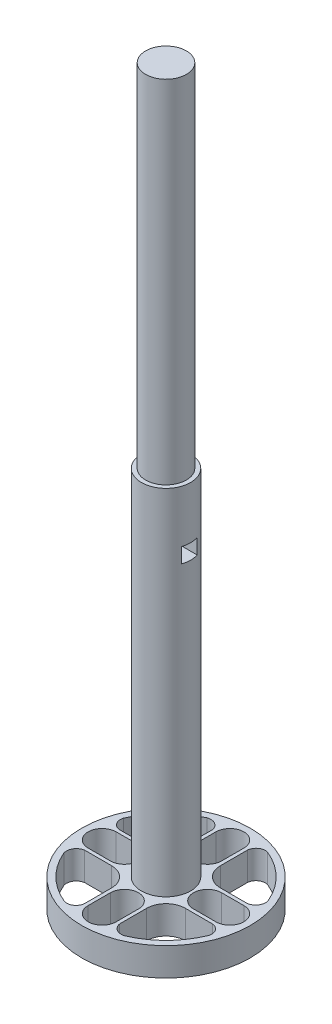
SolidWorks part; units mm, degrees
ref_plane "Front Plane" through (0, 0, 0) normal (0, 0, 1) x (1, 0, 0)
ref_plane "Top Plane" through (0, 0, 0) normal (0, 1, 0) x (1, 0, 0)
ref_plane "Right Plane" through (0, 0, 0) normal (1, 0, 0) x (0, 0, -1)
sketch "Sketch1" plane through (0, 0, 0) normal (0, 1, 0) x (1, 0, 0)
  line L0 (0, -9.0866) -> (0, -5.9134) construction
  line L1 (-9.0866, 0) -> (-5.9134, 0) construction
  line L2 (0, -13.2) -> (0, 13.2) construction
  line L3 (-2, -9.0866) -> (-2, -5.9134)
  line L4 (2, -9.0866) -> (2, -5.9134)
  line L5 (-9.0866, 2) -> (-5.9134, 2)
  line L6 (-9.0866, -2) -> (-5.9134, -2)
  line L7 (0, 9.0866) -> (0, 5.9134) construction
  line L8 (2, 9.0866) -> (2, 5.9134)
  line L9 (-2, 9.0866) -> (-2, 5.9134)
  line L10 (9.0866, 0) -> (5.9134, 0) construction
  line L11 (9.0866, -2) -> (5.9134, -2)
  line L12 (9.0866, 2) -> (5.9134, 2)
  line L13 (-5.2554, -2.5) -> (-7.5, -2.5)
  line L14 (2.5, -5.2554) -> (2.5, -7.5)
  line L15 (-2.5, -7.5) -> (-2.5, -5.2564)
  line L16 (7.5, -2.5) -> (5.2564, -2.5)
  line L17 (2.5, -7.5) -> (2.5, -9.0866)
  line L18 (7.5, -2.5) -> (9.1077, -2.5)
  line L19 (-7.5, -2.5) -> (-9.0866, -2.5)
  line L20 (-2.5, -7.5) -> (-2.5, -9.1077)
  line L21 (-2.5, -5.2564) -> (-2.5, -5.2554)
  line L22 (-2.5, 5.2554) -> (-2.5, 7.5)
  line L23 (-7.5, 2.5) -> (-5.2564, 2.5)
  line L24 (-2.5, 7.5) -> (-2.5, 9.0866)
  line L25 (-7.5, 2.5) -> (-9.1077, 2.5)
  line L26 (-5.2564, 2.5) -> (-5.2554, 2.5)
  line L27 (5.2554, 2.5) -> (7.5, 2.5)
  line L28 (2.5, 7.5) -> (2.5, 5.2564)
  line L29 (5.2564, -2.5) -> (5.2554, -2.5)
  line L30 (7.5, 2.5) -> (9.0866, 2.5)
  line L31 (2.5, 7.5) -> (2.5, 9.1077)
  line L32 (2.5, 5.2564) -> (2.5, 5.2554)
  circle A0 centre (0, 0) radius 3
  arc A1 (-9.0866, 2) -> (-9.0866, -2) centre (-9.0866, 0) ccw
  circle A2 centre (0, 0) radius 12
  arc A3 (-5.9134, -2) -> (-5.9134, 2) centre (-5.9134, 0) ccw
  arc A4 (-2, -9.0866) -> (2, -9.0866) centre (0, -9.0866) ccw
  arc A5 (2, -5.9134) -> (-2, -5.9134) centre (0, -5.9134) ccw
  arc A6 (2, 9.0866) -> (-2, 9.0866) centre (0, 9.0866) ccw
  arc A7 (-2, 5.9134) -> (2, 5.9134) centre (0, 5.9134) ccw
  arc A8 (9.0866, -2) -> (9.0866, 2) centre (9.0866, 0) ccw
  arc A9 (5.9134, 2) -> (5.9134, -2) centre (5.9134, 0) ccw
  arc A10 (-10.197, -4.3513) -> (-4.1974, -10.2613) centre (0, 0) ccw
  arc A11 (4.3513, -10.197) -> (10.2613, -4.1974) centre (0, 0) ccw
  arc A12 (2.5, -5.2554) -> (5.2554, -2.5) centre (5.242, -5.242) cw
  arc A13 (2.5, -9.0866) -> (4.3513, -10.197) centre (3.895, -8.8594) ccw
  arc A14 (9.1077, -2.5) -> (10.2613, -4.1974) centre (8.9969, -3.816) cw
  arc A15 (-5.2554, -2.5) -> (-2.5, -5.2554) centre (-5.242, -5.242) cw
  arc A16 (-9.0866, -2.5) -> (-10.197, -4.3513) centre (-8.8594, -3.895) ccw
  arc A17 (-2.5, -9.1077) -> (-4.1974, -10.2613) centre (-3.816, -8.9969) cw
  arc A18 (-4.3513, 10.197) -> (-10.2613, 4.1974) centre (0, 0) ccw
  arc A19 (-2.5, 5.2554) -> (-5.2554, 2.5) centre (-5.242, 5.242) cw
  arc A20 (-2.5, 9.0866) -> (-4.3513, 10.197) centre (-3.895, 8.8594) ccw
  arc A21 (-9.1077, 2.5) -> (-10.2613, 4.1974) centre (-8.9969, 3.816) cw
  arc A22 (10.197, 4.3513) -> (4.1974, 10.2613) centre (0, 0) ccw
  arc A23 (5.2554, 2.5) -> (2.5, 5.2554) centre (5.242, 5.242) cw
  arc A24 (9.0866, 2.5) -> (10.197, 4.3513) centre (8.8594, 3.895) ccw
  arc A25 (2.5, 9.1077) -> (4.1974, 10.2613) centre (3.816, 8.9969) cw
  point P10 (0, -7.5)
  point P16 (2, -8.0617)
  point P19 (-7.5, 0)
  point P26 (0, 7.5)
  point P33 (7.5, 0)
  point P38 (0, 0)
  point P87 (0, 0)
  point P88 (0, 0)
  point P92 (0, 0)
  dimension "D1" = 4
extrude "Boss-Extrude1" add sketch "Sketch1" along normal blind 4
sketch "Sketch2" plane through (0, 4, 0) normal (0, 1, 0) x (1, 0, 0)
  circle A0 centre (0, 0) radius 3.5
extrude "Boss-Extrude2" add sketch "Sketch2" along normal blind 50.3496
sketch "Sketch3" plane through (0, 0, 0) normal (1, 0, 0) x (0, 0, -1)
  line L0 (0, 13.2) -> (0, -13.2) construction
  line L1 (-1.1122, 44.7759) -> (1.1122, 44.7759)
  line L2 (-1.1122, 44.7759) -> (-1.1122, 46.9235)
  line L3 (-1.1122, 46.9235) -> (1.1122, 46.9235)
  line L4 (1.1122, 44.7759) -> (1.1122, 46.9235)
  line L5 (-1.1122, 44.7759) -> (1.1122, 46.9235) construction
  line L6 (-1.1122, 46.9235) -> (1.1122, 44.7759) construction
  point P0 (0, 45.8497)
extrude "Cut-Extrude1" cut sketch "Sketch3" against normal blind 100 and the other way blind 4.4366
sketch "Sketch10" plane through (0, 54.3496, 0) normal (0, 1, 0) x (1, 0, 0)
  circle A0 centre (0, 0) radius 2.9
extrude "Boss-Extrude3" add sketch "Sketch10" along normal blind 50
sketch "Sketch9" plane through (0, 0, 0) normal (0, 0, 1) x (1, 0, 0)
  line L1 (-1.1122, 44.7759) -> (1.1122, 44.7759)
  line L2 (-1.1122, 44.7759) -> (-1.1122, 46.9235)
  line L3 (-1.1122, 46.9235) -> (1.1122, 46.9235)
  line L4 (1.1122, 44.7759) -> (1.1122, 46.9235)
  line L5 (-1.1122, 44.7759) -> (1.1122, 46.9235) construction
  line L6 (-1.1122, 46.9235) -> (1.1122, 44.7759) construction
  point P0 (0, 45.8497)
